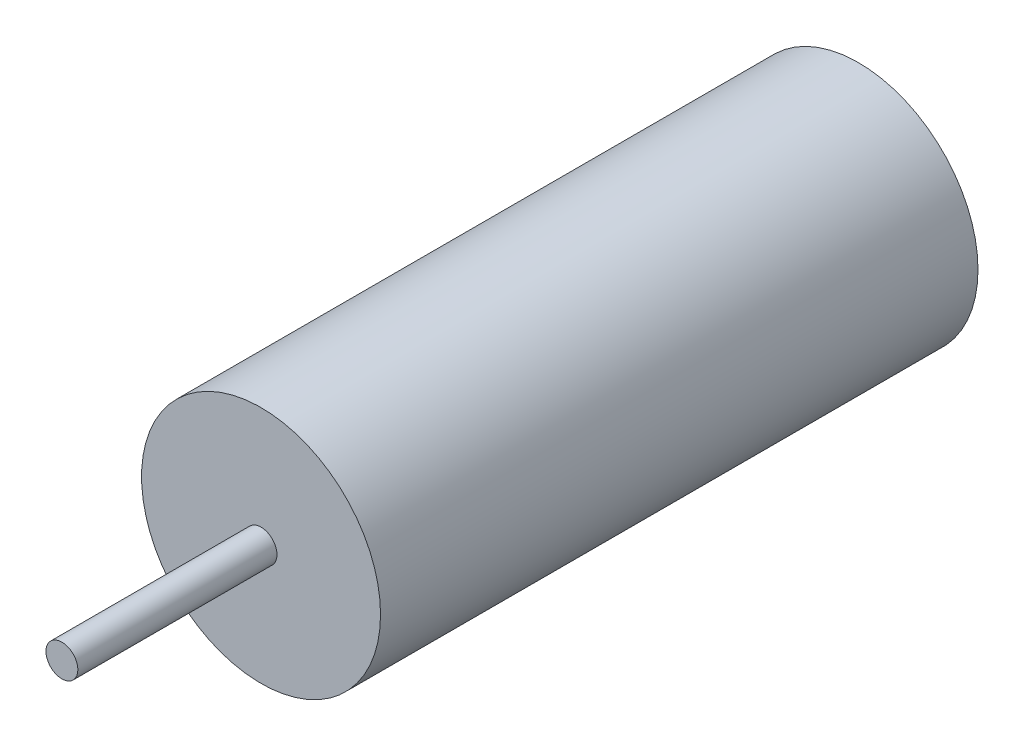
SolidWorks part; units mm, degrees
ref_plane "Front Plane" through (0, 0, 0) normal (0, 0, 1) x (1, 0, 0)
ref_plane "Top Plane" through (0, 0, 0) normal (0, 1, 0) x (1, 0, 0)
ref_plane "Right Plane" through (0, 0, 0) normal (1, 0, 0) x (0, 0, -1)
sketch "Sketch1" plane through (0, 0, 0) normal (0, 0, 1) x (1, 0, 0)
  circle A0 centre (0, 0) radius 3
  dimension "D1" = 6
extrude "Boss-Extrude1" add sketch "Sketch1" along normal blind 15
sketch "Sketch2" plane through (0, 0, 15) normal (0, 0, 1) x (1, 0, 0)
  circle A0 centre (0, 0) radius 0.4
  dimension "D1" = 0.8
extrude "Boss-Extrude2" add sketch "Sketch2" along normal blind 5
